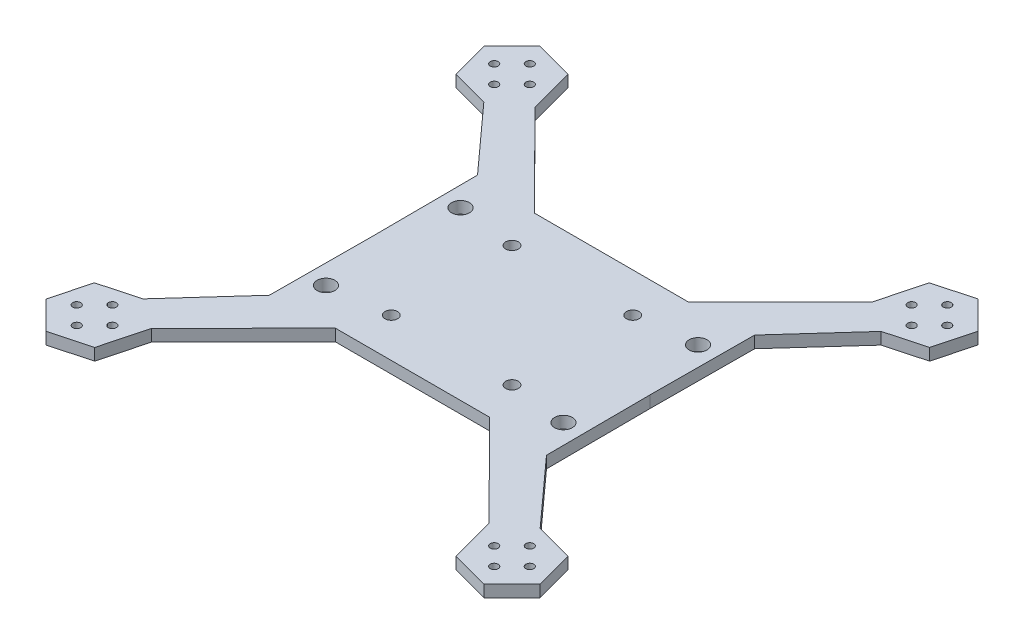
SolidWorks part; units mm, degrees
ref_plane "Front Plane" through (0, 0, 0) normal (0, 0, 1) x (1, 0, 0)
ref_plane "Top Plane" through (0, 0, 0) normal (0, 1, 0) x (1, 0, 0)
ref_plane "Right Plane" through (0, 0, 0) normal (1, 0, 0) x (0, 0, -1)
sketch "Sketch1" plane through (0, 0, 0) normal (0, 1, 0) x (1, 0, 0)
  line L5 (-35, -35) -> (42.6186, 42.6186) construction
  line L6 (-35, 35) -> (35, -35) construction
  line L9 (0, 0) -> (42.4264, 42.4264) construction
  line L10 (52.7307, 48.2307) -> (52.7307, 57.2307) construction
  line L11 (30, 17) -> (30, 0) construction
  line L12 (0, 0) -> (0, 23.6863) construction
  line L28 (0, 0) -> (-174.2372, 0) construction
  line L41 (31.9599, 25.1581) -> (-25.1581, 25.1581) construction
  line L70 (42.6186, 48.4021) -> (19.4638, 25.1581)
  line L72 (48.2307, 52.7307) -> (57.2307, 52.7307) construction
  line L74 (48.2307, 52.7307) -> (52.7307, 48.2307) construction
  line L75 (55.3003, 62.3949) -> (45.646, 59.7881)
  line L77 (45.646, 59.7881) -> (42.6186, 48.4021)
  line L80 (50.185, 43.0729) -> (59.8153, 45.6732)
  line L83 (59.8153, 45.6732) -> (62.3849, 55.3374)
  line L85 (62.3849, 55.3374) -> (55.3003, 62.3949)
  line L87 (50.185, 43.0729) -> (35, 26.2883)
  line L88 (35, 26.2883) -> (34.873, 0)
  line L89 (34.873, -11.873) -> (34.873, 11.873) construction
  line L90 (-21.8355, 25.1581) -> (21.8355, 25.1581)
  line L94 (35, -26.2883) -> (34.873, 0)
  line L100 (48.2307, -52.7307) -> (52.7307, -48.2307) construction
  line L101 (48.2307, -52.7307) -> (57.2307, -52.7307) construction
  line L102 (52.7307, -48.2307) -> (52.7307, -57.2307) construction
  line L106 (62.3849, -55.3374) -> (55.3003, -62.3949)
  line L111 (59.8153, -45.6732) -> (62.3849, -55.3374)
  line L115 (50.185, -43.0729) -> (59.8153, -45.6732)
  line L116 (45.646, -59.7881) -> (42.6186, -48.4021)
  line L119 (55.3003, -62.3949) -> (45.646, -59.7881)
  line L127 (50.185, -43.0729) -> (35, -26.2883)
  line L128 (35, 26.2883) -> (34.873, 0)
  line L129 (35, -26.2883) -> (34.873, 0)
  line L135 (42.6186, -48.4021) -> (19.4638, -25.1581)
  line L138 (40.4517, 52.7386) -> (49.1512, 44.0725) [skipped]
  line L139 (-21.8355, -25.1581) -> (21.8355, -25.1581)
  line L140 (-48.2307, 52.7307) -> (-52.7307, 48.2307) construction
  line L141 (-48.2307, 52.7307) -> (-57.2307, 52.7307) construction
  line L142 (-52.7307, 48.2307) -> (-52.7307, 57.2307) construction
  line L143 (-62.3849, 55.3374) -> (-55.3003, 62.3949)
  line L144 (-59.8153, 45.6732) -> (-62.3849, 55.3374)
  line L145 (-50.185, 43.0729) -> (-59.8153, 45.6732)
  line L146 (-45.646, 59.7881) -> (-42.6186, 48.4021)
  line L147 (-55.3003, 62.3949) -> (-45.646, 59.7881)
  line L148 (-50.185, 43.0729) -> (-35, 26.2883)
  line L149 (-42.6186, 48.4021) -> (-19.4638, 25.1581)
  line L150 (-35, 26.2883) -> (-34.873, 0)
  line L151 (-35, -26.2883) -> (-34.873, 0)
  line L152 (-50.185, -43.0729) -> (-35, -26.2883)
  line L153 (-42.6186, -48.4021) -> (-19.4638, -25.1581)
  line L154 (-52.7307, -48.2307) -> (-52.7307, -57.2307) construction
  line L155 (-48.2307, -52.7307) -> (-57.2307, -52.7307) construction
  line L156 (-48.2307, -52.7307) -> (-52.7307, -48.2307) construction
  line L157 (-55.3003, -62.3949) -> (-45.646, -59.7881)
  line L158 (-45.646, -59.7881) -> (-42.6186, -48.4021)
  line L159 (-50.185, -43.0729) -> (-59.8153, -45.6732)
  line L160 (-59.8153, -45.6732) -> (-62.3849, -55.3374)
  line L161 (-62.3849, -55.3374) -> (-55.3003, -62.3949)
  circle A0 centre (-15.25, 15.25) radius 1.6
  circle A1 centre (15.25, 15.25) radius 1.6
  circle A2 centre (15.25, -15.25) radius 1.6
  circle A3 centre (-15.25, -15.25) radius 1.6
  circle A18 centre (30, 17) radius 2.25
  circle A19 centre (30, -17) radius 2.25
  circle A20 centre (-30, -17) radius 2.25
  circle A21 centre (-30, 17) radius 2.25
  circle A69 centre (52.7307, 52.7307) radius 8.6603 construction
  circle A70 centre (52.7307, 57.2307) radius 1
  circle A71 centre (52.7307, 48.2307) radius 1
  circle A72 centre (48.2307, 52.7307) radius 1
  circle A73 centre (57.2307, 52.7307) radius 1
  circle A124 centre (52.7307, -52.7307) radius 8.6603 construction
  circle A125 centre (57.2307, -52.7307) radius 1
  circle A126 centre (48.2307, -52.7307) radius 1
  circle A127 centre (52.7307, -48.2307) radius 1
  circle A128 centre (52.7307, -57.2307) radius 1
  circle A129 centre (-52.7307, 52.7307) radius 8.6603 construction
  circle A130 centre (-57.2307, 52.7307) radius 1
  circle A131 centre (-48.2307, 52.7307) radius 1
  circle A132 centre (-52.7307, 48.2307) radius 1
  circle A133 centre (-52.7307, 57.2307) radius 1
  circle A134 centre (-52.7307, -52.7307) radius 8.6603 construction
  circle A135 centre (-52.7307, -57.2307) radius 1
  circle A136 centre (-52.7307, -48.2307) radius 1
  circle A137 centre (-48.2307, -52.7307) radius 1
  circle A138 centre (-57.2307, -52.7307) radius 1
  point P0 (0, 0)
  point P8 (52.7307, 52.7307)
  point P9 (52.7307, 52.7307)
  point P17 (0, 0)
  point P45 (24.8566, 0)
  point P47 (30, 0)
  point P90 (0, 25.1581)
  point P95 (0, -25.1581)
  point P96 (0, 25.1581)
  point P99 (0, 25.1581)
  point P110 (0, -25.1581)
  point P118 (0, 0)
  point P126 (0, -25.1581)
  dimension "D3" = 3.2
  dimension "D16" = 4.5
  dimension "D1" = 70
  dimension "D2" = 4.5
  dimension "D4" = 30.5
  dimension "D6" = 4.5
  dimension "D7" = 20
  dimension "D15" = 17
  dimension "D12" = 30
  dimension "D5" = 4
  dimension "D17" = 2
extrude "Boss-Extrude1" add sketch "Sketch1" along normal blind 3
